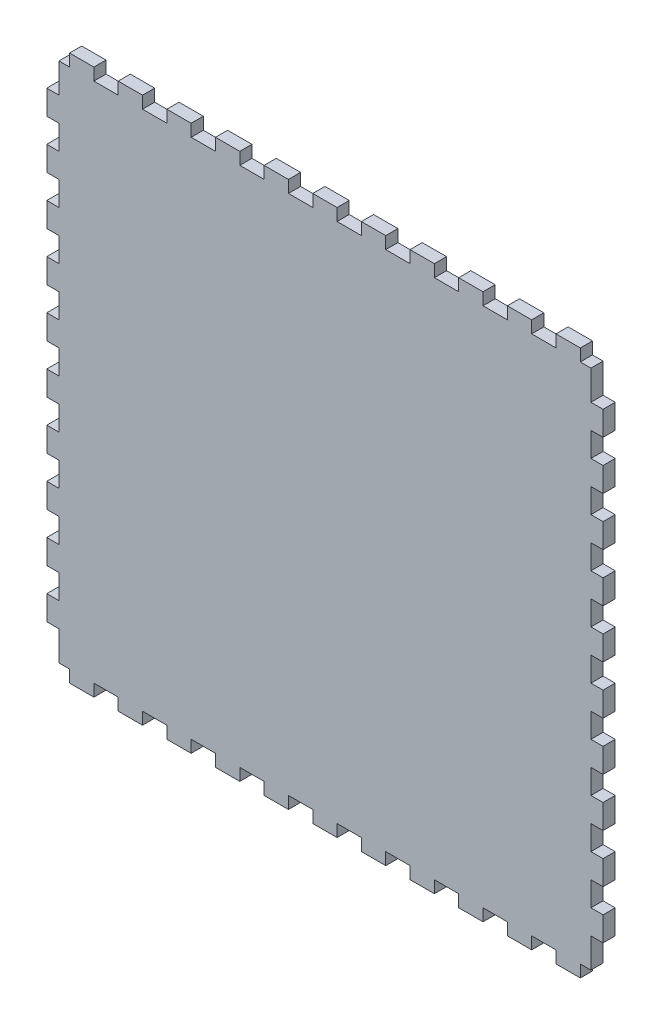
SolidWorks part; units mm, degrees
ref_plane "Front Plane" through (0, 0, 0) normal (0, 0, 1) x (1, 0, 0)
ref_plane "Top Plane" through (0, 0, 0) normal (0, 1, 0) x (1, 0, 0)
ref_plane "Right Plane" through (0, 0, 0) normal (1, 0, 0) x (0, 0, -1)
sketch "Model" plane through (0, 0, 0) normal (0, 0, 1) x (1, 0, 0)
  line L344 (544.6878, 28.9154) -> (549.6738, 28.9154)
  line L345 (549.6738, 28.9154) -> (549.6738, 23.2006)
  line L346 (549.6738, 23.2006) -> (561.1063, 23.2006)
  line L347 (561.1063, 23.2006) -> (561.1063, 28.9154)
  line L348 (561.1063, 28.9154) -> (572.5338, 28.9154)
  line L349 (572.5338, 28.9154) -> (572.5338, 23.2006)
  line L350 (572.5338, 23.2006) -> (583.9638, 23.2006)
  line L351 (583.9638, 23.2006) -> (583.9638, 28.9154)
  line L352 (583.9638, 28.9154) -> (595.3938, 28.9154)
  line L353 (595.3938, 28.9154) -> (595.3938, 23.2006)
  line L354 (595.3938, 23.2006) -> (606.8238, 23.2006)
  line L355 (606.8238, 23.2006) -> (606.8238, 28.9154)
  line L356 (606.8238, 28.9154) -> (618.2563, 28.9154)
  line L357 (618.2563, 28.9154) -> (618.2563, 23.2006)
  line L358 (618.2563, 23.2006) -> (629.6838, 23.2006)
  line L359 (629.6838, 23.2006) -> (629.6838, 28.9154)
  line L360 (629.6838, 28.9154) -> (641.1138, 28.9154)
  line L361 (641.1138, 28.9154) -> (641.1138, 23.2006)
  line L362 (641.1138, 23.2006) -> (652.5438, 23.2006)
  line L363 (652.5438, 23.2006) -> (652.5438, 28.9154)
  line L364 (652.5438, 28.9154) -> (663.9738, 28.9154)
  line L365 (663.9738, 28.9154) -> (663.9738, 23.2006)
  line L366 (663.9738, 23.2006) -> (675.4063, 23.2006)
  line L367 (675.4063, 23.2006) -> (675.4063, 28.9154)
  line L368 (675.4063, 28.9154) -> (686.8338, 28.9154)
  line L369 (686.8338, 28.9154) -> (686.8338, 23.2006)
  line L370 (686.8338, 23.2006) -> (698.2638, 23.2006)
  line L371 (698.2638, 23.2006) -> (698.2638, 28.9154)
  line L372 (698.2638, 28.9154) -> (709.6938, 28.9154)
  line L373 (709.6938, 28.9154) -> (709.6938, 23.2006)
  line L374 (709.6938, 23.2006) -> (721.1238, 23.2006)
  line L375 (721.1238, 23.2006) -> (721.1238, 28.9154)
  line L376 (721.1238, 28.9154) -> (732.5563, 28.9154)
  line L377 (732.5563, 28.9154) -> (732.5563, 23.2006)
  line L378 (732.5563, 23.2006) -> (743.9838, 23.2006)
  line L379 (743.9838, 23.2006) -> (743.9838, 28.9154)
  line L380 (743.9838, 28.9154) -> (755.4138, 28.9154)
  line L381 (755.4138, 28.9154) -> (755.4138, 23.2006)
  line L382 (755.4138, 23.2006) -> (766.8438, 23.2006)
  line L383 (766.8438, 23.2006) -> (766.8438, 28.9154)
  line L384 (766.8438, 28.9154) -> (778.2738, 28.9154)
  line L385 (778.2738, 28.9154) -> (778.2738, 23.2006)
  line L386 (778.2738, 23.2006) -> (789.7063, 23.2006)
  line L387 (789.7063, 23.2006) -> (789.7063, 28.9154)
  line L388 (789.7063, 28.9154) -> (794.6873, 28.9154)
  line L389 (794.6873, 28.9154) -> (794.6873, 42.8308)
  line L390 (794.6873, 42.8308) -> (800.4023, 42.8308)
  line L391 (800.4023, 42.8308) -> (800.4023, 54.2605)
  line L392 (800.4023, 54.2605) -> (794.6873, 54.2605)
  line L393 (794.6873, 54.2605) -> (794.6873, 65.691)
  line L394 (794.6873, 65.691) -> (800.4023, 65.691)
  line L395 (800.4023, 65.691) -> (800.4023, 77.1205)
  line L396 (800.4023, 77.1205) -> (794.6873, 77.1205)
  line L397 (794.6873, 77.1205) -> (794.6873, 88.55)
  line L398 (794.6873, 88.55) -> (800.4023, 88.55)
  line L399 (800.4023, 88.55) -> (800.4023, 99.9807)
  line L400 (800.4023, 99.9807) -> (794.6873, 99.9807)
  line L401 (794.6873, 99.9807) -> (794.6873, 111.4105)
  line L402 (794.6873, 111.4105) -> (800.4023, 111.4105)
  line L403 (800.4023, 111.4105) -> (800.4023, 122.841)
  line L404 (800.4023, 122.841) -> (794.6873, 122.841)
  line L405 (794.6873, 122.841) -> (794.6873, 134.2705)
  line L406 (794.6873, 134.2705) -> (800.4023, 134.2705)
  line L407 (800.4023, 134.2705) -> (800.4023, 145.7)
  line L408 (800.4023, 145.7) -> (794.6873, 145.7)
  line L409 (794.6873, 145.7) -> (794.6873, 157.1308)
  line L410 (794.6873, 157.1308) -> (800.4023, 157.1308)
  line L411 (800.4023, 157.1308) -> (800.4023, 168.5605)
  line L412 (800.4023, 168.5605) -> (794.6873, 168.5605)
  line L413 (794.6873, 168.5605) -> (794.6873, 179.991)
  line L414 (794.6873, 179.991) -> (800.4023, 179.991)
  line L415 (800.4023, 179.991) -> (800.4023, 191.4205)
  line L416 (800.4023, 191.4205) -> (794.6873, 191.4205)
  line L417 (794.6873, 191.4205) -> (794.6873, 202.85)
  line L418 (794.6873, 202.85) -> (800.4023, 202.85)
  line L419 (800.4023, 202.85) -> (800.4023, 214.2807)
  line L420 (800.4023, 214.2807) -> (794.6873, 214.2807)
  line L421 (794.6873, 214.2807) -> (794.6873, 225.7105)
  line L422 (794.6873, 225.7105) -> (800.4023, 225.7105)
  line L423 (800.4023, 225.7105) -> (800.4023, 237.141)
  line L424 (800.4023, 237.141) -> (794.6873, 237.141)
  line L425 (794.6873, 237.141) -> (794.6873, 248.5705)
  line L426 (794.6873, 248.5705) -> (800.4023, 248.5705)
  line L427 (800.4023, 248.5705) -> (800.4023, 259.9995)
  line L428 (800.4023, 259.9995) -> (794.6873, 259.9995)
  line L429 (794.6873, 259.9995) -> (794.6873, 273.9161)
  line L430 (794.6873, 273.9161) -> (789.7063, 273.9161)
  line L431 (789.7063, 273.9161) -> (789.7063, 279.6311)
  line L432 (789.7063, 279.6311) -> (778.2738, 279.6311)
  line L433 (778.2738, 279.6311) -> (778.2738, 273.9161)
  line L434 (778.2738, 273.9161) -> (766.8438, 273.9161)
  line L435 (766.8438, 273.9161) -> (766.8438, 279.6311)
  line L436 (766.8438, 279.6311) -> (755.4138, 279.6311)
  line L437 (755.4138, 279.6311) -> (755.4138, 273.9161)
  line L438 (755.4138, 273.9161) -> (743.9838, 273.9161)
  line L439 (743.9838, 273.9161) -> (743.9838, 279.6311)
  line L440 (743.9838, 279.6311) -> (732.5563, 279.6311)
  line L441 (732.5563, 279.6311) -> (732.5563, 273.9161)
  line L442 (732.5563, 273.9161) -> (721.1238, 273.9161)
  line L443 (721.1238, 273.9161) -> (721.1238, 279.6311)
  line L444 (721.1238, 279.6311) -> (709.6938, 279.6311)
  line L445 (709.6938, 279.6311) -> (709.6938, 273.9161)
  line L446 (709.6938, 273.9161) -> (698.2638, 273.9161)
  line L447 (698.2638, 273.9161) -> (698.2638, 279.6311)
  line L448 (698.2638, 279.6311) -> (686.8338, 279.6311)
  line L449 (686.8338, 279.6311) -> (686.8338, 273.9161)
  line L450 (686.8338, 273.9161) -> (675.4063, 273.9161)
  line L451 (675.4063, 273.9161) -> (675.4063, 279.6311)
  line L452 (675.4063, 279.6311) -> (663.9738, 279.6311)
  line L453 (663.9738, 279.6311) -> (663.9738, 273.9161)
  line L454 (663.9738, 273.9161) -> (652.5438, 273.9161)
  line L455 (652.5438, 273.9161) -> (652.5438, 279.6311)
  line L456 (652.5438, 279.6311) -> (641.1138, 279.6311)
  line L457 (641.1138, 279.6311) -> (641.1138, 273.9161)
  line L458 (641.1138, 273.9161) -> (629.6838, 273.9161)
  line L459 (629.6838, 273.9161) -> (629.6838, 279.6311)
  line L460 (629.6838, 279.6311) -> (618.2563, 279.6311)
  line L461 (618.2563, 279.6311) -> (618.2563, 273.9161)
  line L462 (618.2563, 273.9161) -> (606.8238, 273.9161)
  line L463 (606.8238, 273.9161) -> (606.8238, 279.6311)
  line L464 (606.8238, 279.6311) -> (595.3938, 279.6311)
  line L465 (595.3938, 279.6311) -> (595.3938, 273.9161)
  line L466 (595.3938, 273.9161) -> (583.9638, 273.9161)
  line L467 (583.9638, 273.9161) -> (583.9638, 279.6311)
  line L468 (583.9638, 279.6311) -> (572.5338, 279.6311)
  line L469 (572.5338, 279.6311) -> (572.5338, 273.9161)
  line L470 (572.5338, 273.9161) -> (561.1063, 273.9161)
  line L471 (561.1063, 273.9161) -> (561.1063, 279.6311)
  line L472 (561.1063, 279.6311) -> (549.6738, 279.6311)
  line L473 (549.6738, 279.6311) -> (549.6738, 273.9161)
  line L474 (549.6738, 273.9161) -> (544.6878, 273.9161)
  line L475 (544.6878, 273.9161) -> (544.6878, 259.9995)
  line L476 (544.6878, 259.9995) -> (538.9728, 259.9995)
  line L477 (538.9728, 259.9995) -> (538.9728, 248.5705)
  line L478 (538.9728, 248.5705) -> (544.6878, 248.5705)
  line L479 (544.6878, 248.5705) -> (544.6878, 237.141)
  line L480 (544.6878, 237.141) -> (538.9728, 237.141)
  line L481 (538.9728, 237.141) -> (538.9728, 225.7105)
  line L482 (538.9728, 225.7105) -> (544.6878, 225.7105)
  line L483 (544.6878, 225.7105) -> (544.6878, 214.2807)
  line L484 (544.6878, 214.2807) -> (538.9728, 214.2807)
  line L485 (538.9728, 214.2807) -> (538.9728, 202.85)
  line L486 (538.9728, 202.85) -> (544.6878, 202.85)
  line L487 (544.6878, 202.85) -> (544.6878, 191.4205)
  line L488 (544.6878, 191.4205) -> (538.9728, 191.4205)
  line L489 (538.9728, 191.4205) -> (538.9728, 179.991)
  line L490 (538.9728, 179.991) -> (544.6878, 179.991)
  line L491 (544.6878, 179.991) -> (544.6878, 168.5605)
  line L492 (544.6878, 168.5605) -> (538.9728, 168.5605)
  line L493 (538.9728, 168.5605) -> (538.9728, 157.1308)
  line L494 (538.9728, 157.1308) -> (544.6878, 157.1308)
  line L495 (544.6878, 157.1308) -> (544.6878, 145.7)
  line L496 (544.6878, 145.7) -> (538.9728, 145.7)
  line L497 (538.9728, 145.7) -> (538.9728, 134.2705)
  line L498 (538.9728, 134.2705) -> (544.6878, 134.2705)
  line L499 (544.6878, 134.2705) -> (544.6878, 122.841)
  line L500 (544.6878, 122.841) -> (538.9728, 122.841)
  line L501 (538.9728, 122.841) -> (538.9728, 111.4105)
  line L502 (538.9728, 111.4105) -> (544.6878, 111.4105)
  line L503 (544.6878, 111.4105) -> (544.6878, 99.9807)
  line L504 (544.6878, 99.9807) -> (538.9728, 99.9807)
  line L505 (538.9728, 99.9807) -> (538.9728, 88.55)
  line L506 (538.9728, 88.55) -> (544.6878, 88.55)
  line L507 (544.6878, 88.55) -> (544.6878, 77.1205)
  line L508 (544.6878, 77.1205) -> (538.9728, 77.1205)
  line L509 (538.9728, 77.1205) -> (538.9728, 65.691)
  line L510 (538.9728, 65.691) -> (544.6878, 65.691)
  line L511 (544.6878, 65.691) -> (544.6878, 54.2605)
  line L512 (544.6878, 54.2605) -> (538.9728, 54.2605)
  line L513 (538.9728, 54.2605) -> (538.9728, 42.8308)
  line L514 (538.9728, 42.8308) -> (544.6878, 42.8308)
  line L515 (544.6878, 42.8308) -> (544.6878, 28.9154)
  text T6 "Floor" font "SWTXT" height 4
extrude "Boss-Extrude1" add sketch "Model" along normal blind 5.715 contours L514 L515 L344 L345 L346 L347 L348 L349 L350 L351 L352 L353 L354 L355 L356 L357 L358 L359 L360 L361 L362 L363 L364 L365 L366 L367 L368 L369 L370 L371 L372 L373 L374 L375 L376 L377 L378 L379 L380 L381 L382 L383 L384 L385 L386 L387 L388 L389 L390 L391 L392
